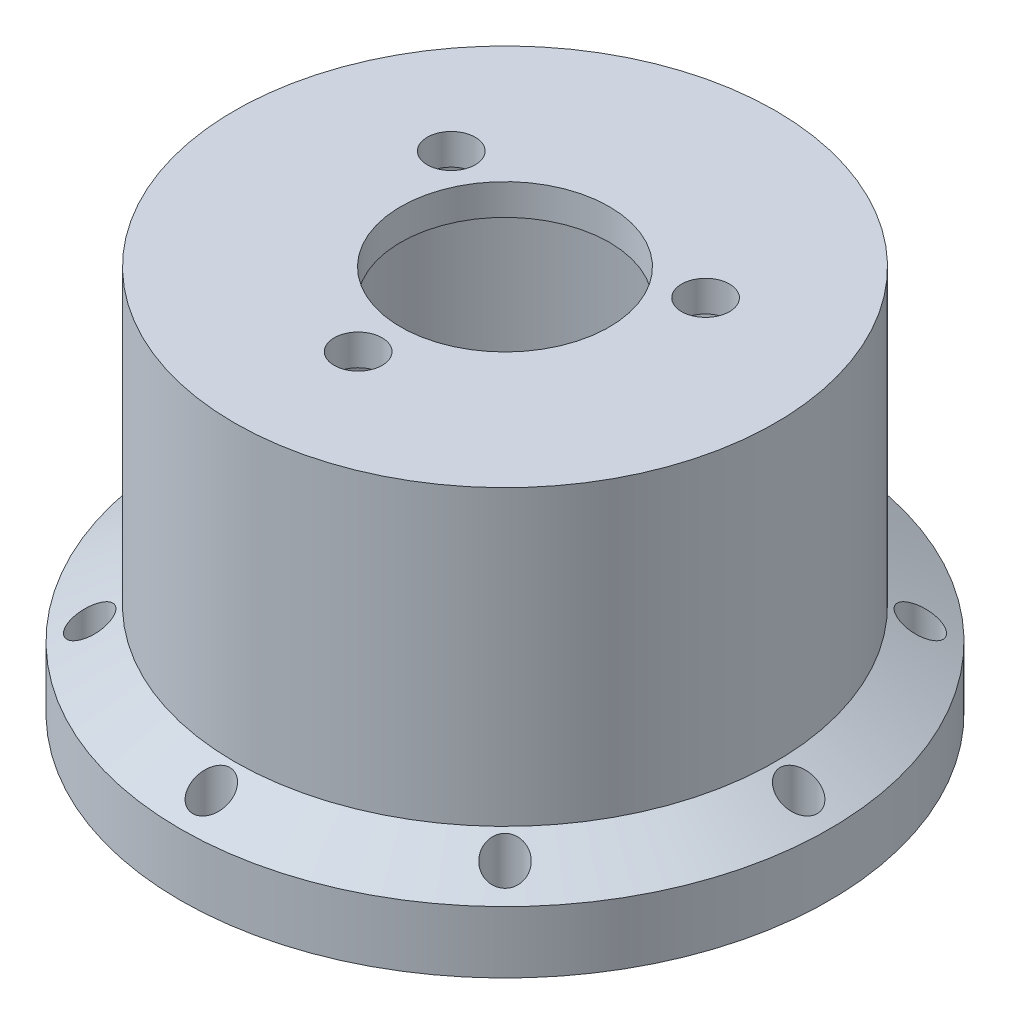
SolidWorks part; units mm, degrees
other "细节项目1"
material "6061-T6 (SS)"
ref_plane "前视基准面" through (0, 0, 0) normal (0, 0, 1) x (1, 0, 0)
ref_plane "上视基准面" through (0, 0, 0) normal (0, 1, 0) x (1, 0, 0)
ref_plane "右视基准面" through (0, 0, 0) normal (1, 0, 0) x (0, 0, -1)
sketch "草图1" plane through (0, 0, 0) normal (0, 0, 1) x (1, 0, 0)
  line L0 (0, 0) -> (0, 36.8725) construction
  line L1 (-16, 0) -> (-17, 0)
  line L2 (-17, 0) -> (-17, 2)
  line L3 (-17, 2) -> (-21, 2)
  line L4 (-21, 2) -> (-21, 6)
  line L5 (-21, 6) -> (-17.5, 8.0207)
  line L6 (-17.5, 8.0207) -> (-17.5, 27)
  line L7 (-17.5, 27) -> (-6.75, 27)
  line L8 (-6.75, 27) -> (-6.75, 25)
  line L9 (-6.75, 25) -> (-16, 25)
  line L10 (-16, 25) -> (-16, 0)
  dimension "D1" = 32
  dimension "D2" = 34
  dimension "D3" = 1.5
  dimension "D4" = 2
  dimension "D5" = 4
  dimension "D6" = 4
  dimension "D7" = 60
  dimension "D8" = 2
  dimension "D9" = 25
  dimension "D10" = 13.5
revolve "旋转1" add sketch "草图1" angle 360 about L0
sketch "草图2" plane through (0, 2, 0) normal (0, -1, 0) x (1, 0, 0)
  circle A0 centre (0, 0) radius 19 construction
  circle A1 centre (0, -19) radius 1.2
  dimension "D1" = 38
  dimension "D2" = 2.4
extrude "切除-拉伸1" cut sketch "草图2" against normal blind 8
cosmetic thread "装饰螺纹线1" parameters "D2"=3
pattern_circular "阵列(圆周)1" count 8 over 360 about axis through (0, 0, 0) along (0, 1, 0) of "切除-拉伸1"
sketch "草图3" plane through (0, 27, 0) normal (0, 1, 0) x (1, 0, 0)
  circle A0 centre (0, 0) radius 9.5 construction
  circle A1 centre (0, -9.5) radius 1.55
  circle A2 centre (-8.2272, 4.75) radius 1.55
  circle A3 centre (8.2272, 4.75) radius 1.55
  point P11 (0, 0)
  dimension "D1" = 19
  dimension "D2" = 3.1
  dimension "D3" = 3
extrude "切除-拉伸2" cut sketch "草图3" against normal blind 10
